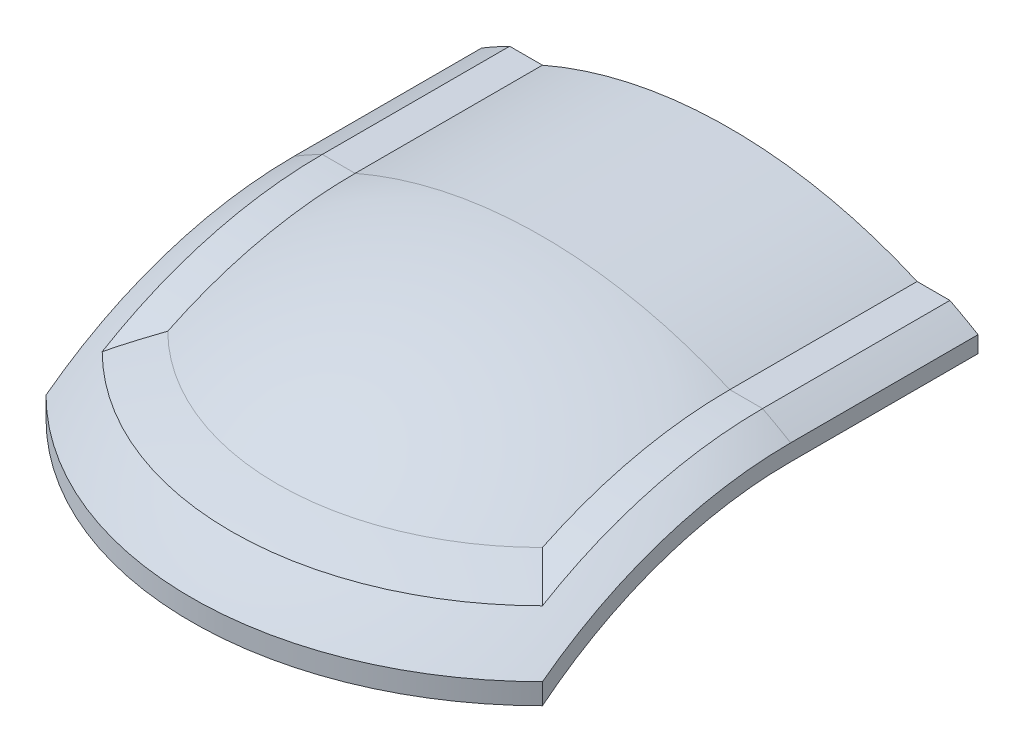
SolidWorks part; units mm, degrees
ref_plane "前视基准面" through (0, 0, 0) normal (0, 0, 1) x (1, 0, 0)
ref_plane "上视基准面" through (0, 0, 0) normal (0, 1, 0) x (1, 0, 0)
ref_plane "右视基准面" through (0, 0, 0) normal (1, 0, 0) x (0, 0, -1)
sketch "草图1" plane through (0, 0, 0) normal (0, 0, 1) x (1, 0, 0)
  line L0 (-50, 0) -> (50, 0)
  line L1 (-50, 0) -> (-50, 200)
  line L2 (50, 0) -> (50, 200)
  line L3 (-53, 0) -> (-53, 200)
  line L4 (53, 0) -> (53, 200)
  line L5 (-47, 91.6515) -> (-40, 91.6515)
  line L6 (47, 91.6515) -> (40, 91.6515)
  arc A0 (-53, 84.7998) -> (53, 84.7998) centre (0, 0) cw
  arc A1 (-50, 83.1204) -> (50, 83.1204) centre (0, 0) cw
  arc A2 (-53, 88.3176) -> (53, 88.3176) centre (0, 0) cw
  point P4 (0, 0)
  point P6 (0, 0)
  point P10 (0, 0)
  dimension "D4" = 3
  dimension "D5" = 97
  dimension "D7" = 100
  dimension "D8" = 103
  dimension "D1" = 100
  dimension "D2" = 200
  dimension "D3" = 200
  dimension "D6" = 3
  dimension "D9" = 3
extrude "平弧" add sketch "草图1" against normal blind 40 contours L1 A1 L2 A0 | A2 L6 A0 L2 | A2 L2 A0 L4 | A2 L1 A0 L5 | A2 L3 A0 L1
sketch "草图5" plane through (0, 0, 0) normal (0, 0, 1) x (1, 0, 0)
  line L0 (-50, 0) -> (50, 0)
  line L6 (-50, 86.6025) -> (-50, 83.1204)
  line L7 (50, 83.1204) -> (50, 86.6025)
  line L8 (53, 84.7998) -> (53, 88.3176)
  line L9 (47, 91.6515) -> (40, 91.6515)
  line L10 (-40, 91.6515) -> (-47, 91.6515)
  line L11 (-53, 88.3176) -> (-53, 84.7998)
  line L12 (-50, 86.6025) -> (-50, 83.1204)
  line L13 (50, 83.1204) -> (50, 86.6025)
  line L14 (53, 84.7998) -> (53, 88.3176)
  line L15 (47, 91.6515) -> (40, 91.6515)
  line L16 (-40, 91.6515) -> (-47, 91.6515)
  line L17 (-53, 88.3176) -> (-53, 84.7998)
  arc A6 (50, 83.1204) -> (-50, 83.1204) centre (0, 0) ccw
  arc A7 (53, 84.7998) -> (50, 86.6025) centre (0, 0) ccw
  arc A8 (53, 88.3176) -> (47, 91.6515) centre (0, 0) ccw
  arc A9 (40, 91.6515) -> (-40, 91.6515) centre (0, 0) ccw
  arc A10 (-47, 91.6515) -> (-53, 88.3176) centre (0, 0) ccw
  arc A11 (-50, 86.6025) -> (-53, 84.7998) centre (0, 0) ccw
  arc A12 (50, 83.1204) -> (-50, 83.1204) centre (0, 0) ccw
  arc A13 (53, 84.7998) -> (50, 86.6025) centre (0, 0) ccw
  arc A14 (53, 88.3176) -> (47, 91.6515) centre (0, 0) ccw
  arc A15 (40, 91.6515) -> (-40, 91.6515) centre (0, 0) ccw
  arc A16 (-47, 91.6515) -> (-53, 88.3176) centre (0, 0) ccw
  arc A17 (-50, 86.6025) -> (-53, 84.7998) centre (0, 0) ccw
  point P20 (0, 0)
  dimension "D2" = 100
  dimension "D1" = 0
revolve "圆弧" add sketch "草图5" angle 90 about L0
sketch "草图6" plane through (0, 0, 0) normal (0, 1, 0) x (1, 0, 0)
  line L0 (0, 0) -> (-84.8528, -84.8528)
  line L1 (-50, -50) -> (50, -50)
  line L2 (-50, -50) -> (-50, 0)
  line L3 (-50, 0) -> (50, 0)
  line L4 (50, -50) -> (50, 0)
  line L5 (-50, -50) -> (50, 0) construction
  line L6 (-50, 0) -> (50, -50) construction
  line L7 (0, 0) -> (84.8528, -84.8528)
  arc A0 (-84.8528, -84.8528) -> (84.8528, -84.8528) centre (0, 0) ccw
  point P0 (0, -25)
  dimension "D1" = 50
  dimension "D2" = 100
  dimension "D3" = 0
  dimension "D4" = 0
  dimension "D5" = 120
  dimension "D6" = 120
extrude "开口" cut sketch "草图6" along normal through all
sketch "草图7" plane through (0, 0, 0) normal (0.7071, 0, 0.7071) x (0.7071, 0, -0.7071)
  line L0 (0, 0) -> (0, 97)
  line L3 (-74.9533, 70.647) -> (-74.9533, 66.1967)
  line L4 (-70.7107, 70.7107) -> (-70.7107, 66.4003)
  line L5 (0, 97) -> (0, 100)
  line L6 (-74.9533, 70.647) -> (-74.9533, 66.1967)
  line L7 (-70.7107, 70.7107) -> (-70.7107, 66.4003)
  line L8 (0, 97) -> (0, 100)
  arc A4 (0, 100) -> (-56.5685, 82.4621) centre (0, 0) ccw
  arc A5 (-66.468, 78.6829) -> (-74.9533, 70.647) centre (0, 0) ccw
  arc A6 (-70.7107, 70.7107) -> (-74.9533, 66.1967) centre (0, 0) ccw
  arc A7 (0, 97) -> (-70.7107, 66.4003) centre (0, 0) ccw
  arc A8 (0, 100) -> (-56.5685, 82.4621) centre (0, 0) ccw
  arc A9 (-66.468, 78.6829) -> (-74.9533, 70.647) centre (0, 0) ccw
  arc A10 (-70.7107, 70.7107) -> (-74.9533, 66.1967) centre (0, 0) ccw
  arc A11 (0, 97) -> (-70.7107, 66.4003) centre (0, 0) ccw
  ellipse E1 centre (0, 0) end of major axis (-129.6148, 0) minor radius 91.6515 (-56.5685, 82.4621) -> (-66.468, 78.6829) ccw
  ellipse E2 centre (0, 0) end of major axis (-129.6148, 0) minor radius 91.6515 (-56.5685, 82.4621) -> (-66.468, 78.6829) ccw
  dimension "D1" = 0
revolve "后弧" add sketch "草图7" angle 90 about L0
